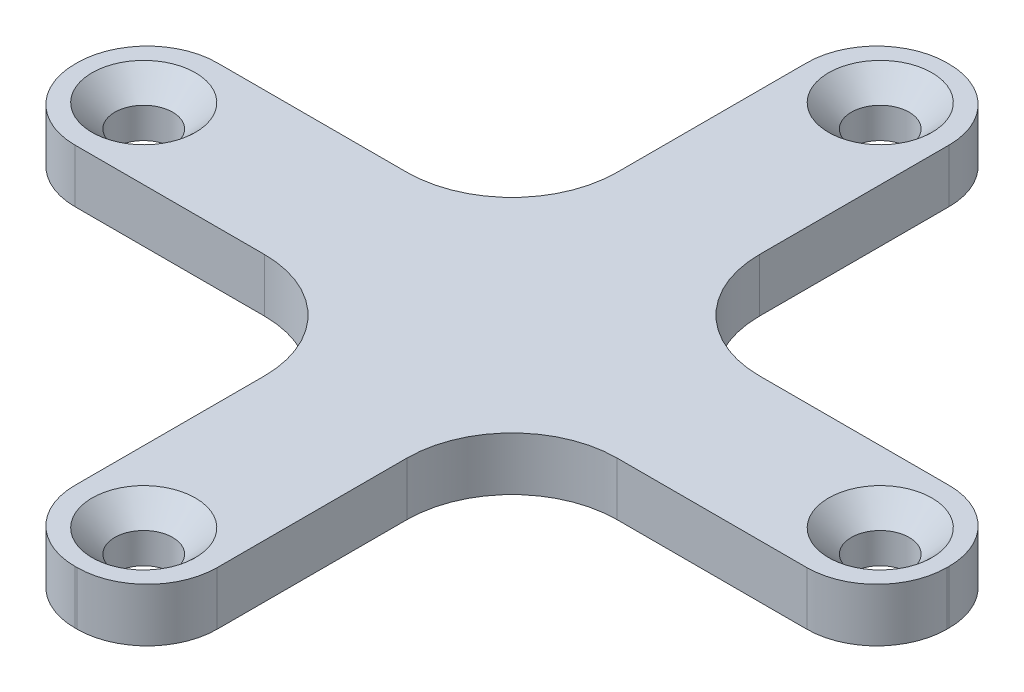
SolidWorks part; units mm, degrees
material "6061 Alloy"
ref_plane "Front" through (0, 0, 0) normal (0, 0, 1) x (1, 0, 0)
ref_plane "Top" through (0, 0, 0) normal (0, 1, 0) x (1, 0, 0)
ref_plane "Right" through (0, 0, 0) normal (1, 0, 0) x (0, 0, -1)
sketch "Sketch1" plane through (0, 0, 0) normal (0, 1, 0) x (1, 0, 0)
  line L0 (0, -9.9812) -> (0, 9.9812) construction
  line L1 (-24.895, 4.064) -> (-4.064, 4.064)
  line L2 (0, 4.064) -> (0, -4.064) construction
  line L3 (-24.895, -4.064) -> (-4.064, -4.064)
  line L4 (24.895, 4.064) -> (24.895, -4.064)
  line L5 (-9.9367, 0) -> (9.9367, 0) construction
  line L6 (0, 0) -> (24.895, 0) construction
  line L7 (0, 24.895) -> (0, -24.895) construction
  line L8 (0, 0) -> (18.4238, 18.4238) construction
  line L9 (4.064, -24.895) -> (4.064, 24.895) construction
  line L10 (4.064, 24.895) -> (-4.064, 24.895)
  line L11 (-4.064, -24.895) -> (-4.064, -4.064)
  line L12 (-24.895, 4.064) -> (-24.895, -4.064)
  line L13 (4.064, -24.895) -> (-4.064, -24.895)
  line L14 (4.064, 4.064) -> (24.895, 4.064)
  line L15 (4.064, -4.064) -> (24.895, -4.064)
  line L16 (-4.064, 4.064) -> (-4.064, 24.895)
  line L17 (4.064, 4.064) -> (4.064, 24.895)
  line L18 (4.064, -4.064) -> (4.064, -24.895)
  line L19 (19.374, 4.064) -> (19.374, -4.064) construction
  circle A0 centre (21.025, 0) radius 1.651
  circle A1 centre (0, 21.025) radius 1.651
  circle A2 centre (-21.025, 0) radius 1.651
  circle A3 centre (0, -21.025) radius 1.651
  point P15 (-4.064, 0)
  point P30 (4.064, 0)
  dimension "D3" = 3.302
  dimension "D4" = 3.87
  dimension "D1" = 8.128
  dimension "D2" = 42.05
extrude "Boss-Extrude1" add sketch "Sketch1" along normal blind 3.048
fillet "Fillet3" radius 4 8 edges at (-4.064, 1.524, -24.895) (4.064, 1.524, -24.895) (24.895, 1.524, -4.064) (24.895, 1.524, 4.064) (4.064, 1.524, 24.895) (-4.064, 1.524, 24.895) (-24.895, 1.524, 4.064) (-24.895, 1.524, -4.064)
chamfer "Chamfer1" distance 1.3 angle 45 4 edges at (0, 3.048, 22.676) (-21.025, 3.048, -1.651) (0, 3.048, -22.676) (21.025, 3.048, 1.651)
fillet "Fillet4" radius 6 4 edges at (-4.064, 1.524, -4.064) (-4.064, 1.524, 4.064) (4.064, 1.524, 4.064) (4.064, 1.524, -4.064)
